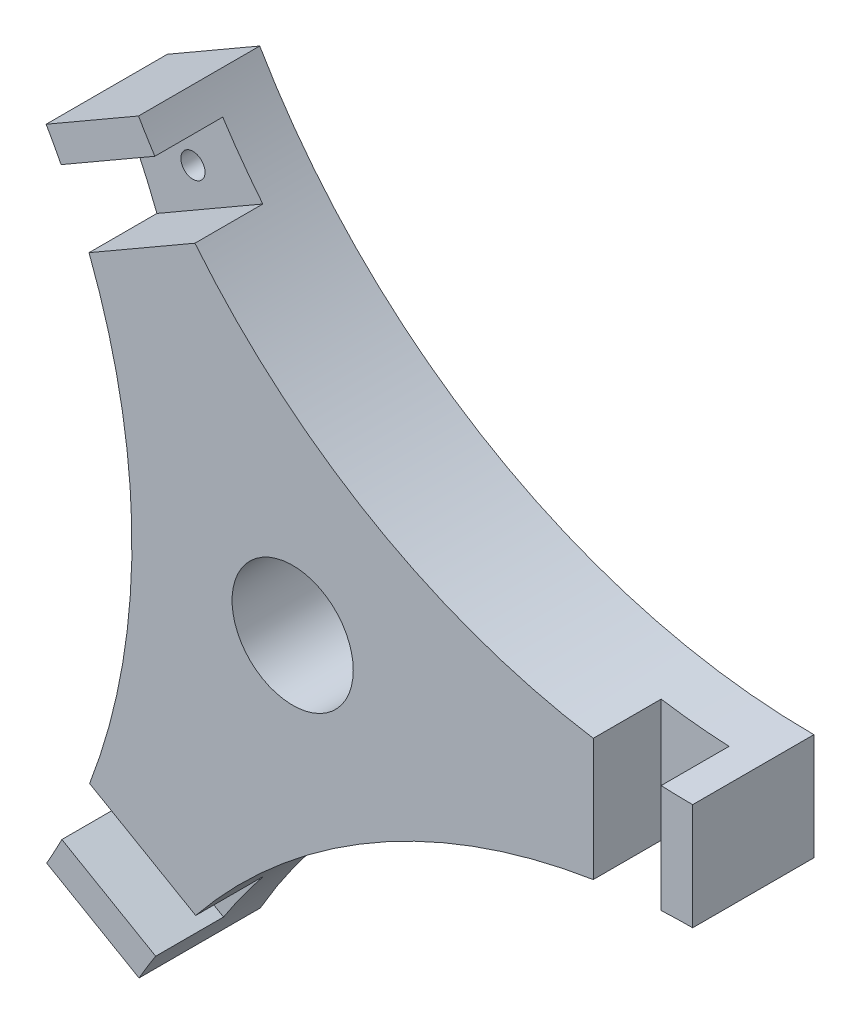
SolidWorks part; units mm, degrees
material "3.1255 (EN-AW 2014)"
ref_plane "Alzado" through (0, 0, 0) normal (0, 0, 1) x (1, 0, 0)
ref_plane "Planta" through (0, 0, 0) normal (0, 1, 0) x (1, 0, 0)
ref_plane "Vista lateral" through (0, 0, 0) normal (1, 0, 0) x (0, 0, -1)
sketch "Croquis1" plane through (0, 0, 0) normal (0, 0, 1) x (1, 0, 0)
  line L0 (41.25, -5.5) -> (41.25, 5.5)
  line L1 (-25.3663, -33.0266) -> (-15.84, -38.5266)
  line L2 (-15.8968, 38.4281) -> (-25.4231, 32.9281)
  circle A0 centre (0, 0) radius 6.25
  circle A1 centre (34.5, 0) radius 1.25
  circle A2 centre (-17.2281, -29.9309) radius 1.25
  circle A3 centre (-17.285, 29.8324) radius 1.25
  arc A4 (-15.84, -38.5266) -> (41.25, -5.5) centre (41.3639, -71.5533) cw
  arc A5 (-25.4231, 32.9281) -> (-25.3663, -33.0266) centre (-82.627, -0.0986) cw
  arc A6 (41.25, 5.5) -> (-15.8968, 38.4281) centre (41.25, 71.5534) cw
  point P18 (-0.0044, -0.0328)
  point P26 (-0.0044, -0.0328)
  dimension "D1" = 34.5
  dimension "D2" = 12.5
  dimension "D3" = 2.5
  dimension "D4" = 11
  dimension "D5" = 5.5
  dimension "D6" = 41.25
  dimension "D7" = 3
  dimension "D8" = 3
extrude "Saliente-Extruir1" add sketch "Croquis1" along normal blind 12.5
sketch "Croquis2" plane through (0, 0, 12.5) normal (0, 0, 1) x (1, 0, 0)
  line L0 (38, 8.8216) -> (31, 8.8216)
  line L1 (38, 8.8216) -> (38, -9.8621)
  line L2 (31, 8.8216) -> (31, -9.8621)
  line L3 (31, -9.8621) -> (38, -9.8621)
  line L4 (-11.3603, -37.3198) -> (-7.8603, -31.2576)
  line L5 (-24.0408, -21.9157) -> (-27.5408, -27.9779)
  line L6 (-11.3603, -37.3198) -> (-27.5408, -27.9779)
  line L7 (-7.8603, -31.2576) -> (-24.0408, -21.9157)
  line L8 (-26.6397, 28.4982) -> (-23.1397, 22.436)
  line L9 (-6.9592, 31.7778) -> (-10.4592, 37.84)
  line L10 (-26.6397, 28.4982) -> (-10.4592, 37.84)
  line L11 (-23.1397, 22.436) -> (-6.9592, 31.7778)
  circle A0 centre (34.5, 0) radius 1.25 construction
  point P17 (0, 0)
  dimension "D2" = 3.5
  dimension "D1" = 7
  dimension "D3" = 3
extrude "Cortar-Extruir1" cut sketch "Croquis2" against normal blind 7
